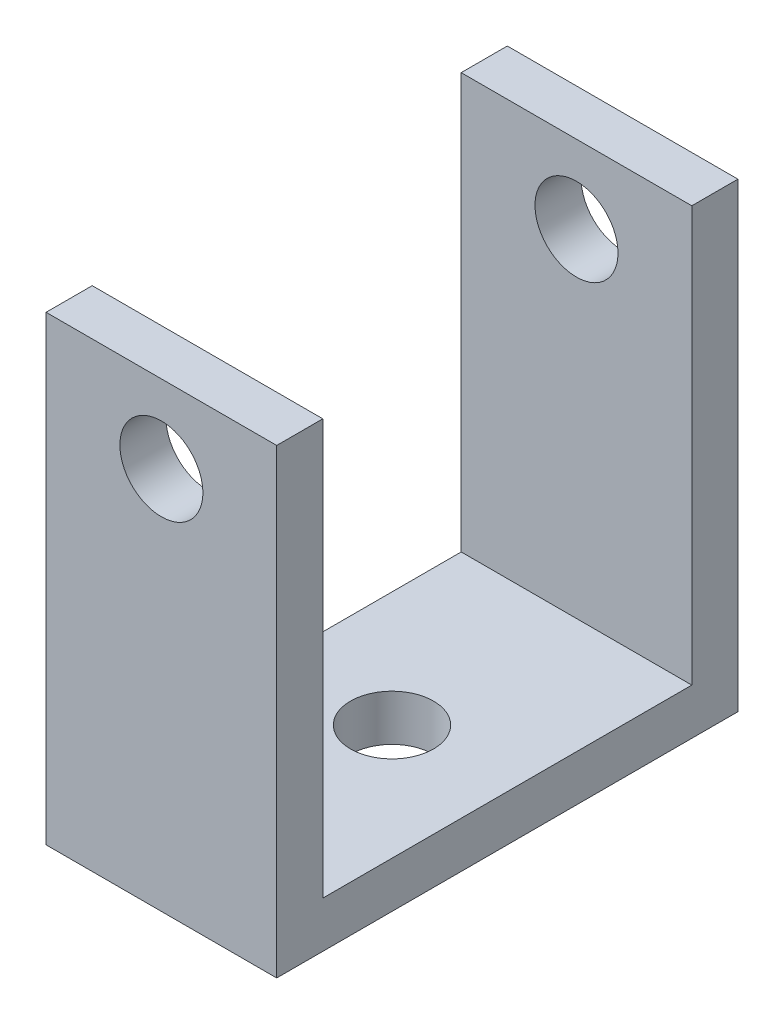
SolidWorks part; units mm, degrees
material "Plain Carbon Steel"
ref_plane "Front XY" through (0, 0, 0) normal (0, 0, 1) x (1, 0, 0)
ref_plane "Top XZ" through (0, 0, 0) normal (0, 1, 0) x (1, 0, 0)
ref_plane "Right YZ" through (0, 0, 0) normal (1, 0, 0) x (0, 0, -1)
sketch "Sketch1" plane through (0, 0, 0) normal (1, 0, 0) x (0, 0, -1)
  line L0 (-12.7, 25.4) -> (12.7, 25.4) construction
  line L1 (-12.7, 0) -> (12.7, 0)
  line L2 (-12.7, 0) -> (-12.7, 25.4)
  line L4 (12.7, 0) -> (12.7, 25.4)
  line L5 (-12.7, 0) -> (12.7, 25.4) construction
  line L6 (-12.7, 25.4) -> (12.7, 0) construction
  point P0 (0, 12.7)
  point P5 (0, 0)
  dimension "D1" = 25.4
  dimension "D2" = 25.4
extrude "Extrude-Thin1" add sketch "Sketch1" along normal mid plane 12.7 thin contours L4 L1 L2 thin type one direction wall 2.54
sketch "Sketch4" plane through (0, 0, 12.7) normal (0, 0, 1) x (1, 0, 0)
  line L0 (0, 0) -> (0, 21.1074) construction
  line L1 (6.35, 25.4) -> (-6.35, 25.4) construction
  circle A0 centre (0, 21.1074) radius 2.286
  dimension "D1" = 4.2926
  dimension "D2" = 4.572
extrude "Cut-Extrude1" cut sketch "Sketch4" against normal through all and the other way through all contours A0
sketch "Sketch5" plane through (0, 2.54, 0) normal (0, 1, 0) x (1, 0, 0)
  circle A0 centre (0, 0) radius 2.286
  dimension "D1" = 4.572
extrude "Cut-Extrude2" cut sketch "Sketch5" against normal through all
